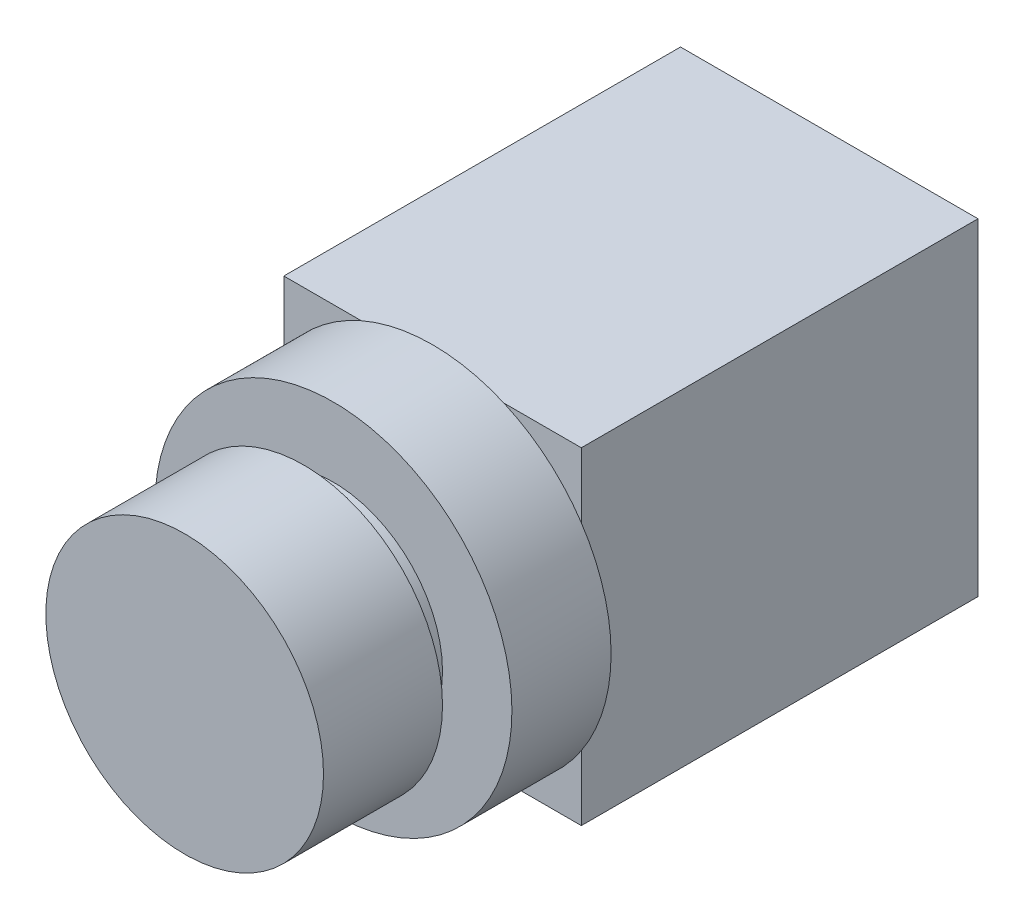
SolidWorks part; units mm, degrees
ref_plane "前视基准面" through (0, 0, 0) normal (0, 0, 1) x (1, 0, 0)
ref_plane "上视基准面" through (0, 0, 0) normal (0, 1, 0) x (1, 0, 0)
ref_plane "右视基准面" through (0, 0, 0) normal (1, 0, 0) x (0, 0, -1)
sketch "草图1" plane through (0, 0, 0) normal (0, 0, 1) x (1, 0, 0)
  circle A0 centre (0, 0) radius 14
extrude "凸台-拉伸1" add sketch "草图1" along normal blind 12
sketch "草图2" plane through (0, 0, 0) normal (0, 0, -1) x (-1, 0, 0)
  circle A0 centre (0, 0) radius 11
extrude "凸台-拉伸2" add sketch "草图2" along normal blind 3
sketch "草图3" plane through (0, 0, -3) normal (0, 0, -1) x (-1, 0, 0)
  circle A0 centre (0, 0) radius 18
extrude "凸台-拉伸3" add sketch "草图3" along normal blind 10
sketch "草图4" plane through (0, 0, -13) normal (0, 0, -1) x (-1, 0, 0)
  line L1 (-15, 16.5) -> (15, 16.5)
  line L2 (-15, 16.5) -> (-15, -16.5)
  line L3 (-15, -16.5) -> (15, -16.5)
  line L4 (15, 16.5) -> (15, -16.5)
  line L5 (-15, 16.5) -> (15, -16.5) construction
  line L6 (-15, -16.5) -> (15, 16.5) construction
  point P3 (0, 0)
extrude "凸台-拉伸4" add sketch "草图4" along normal blind 40 contours L4 L3 L2 L1
